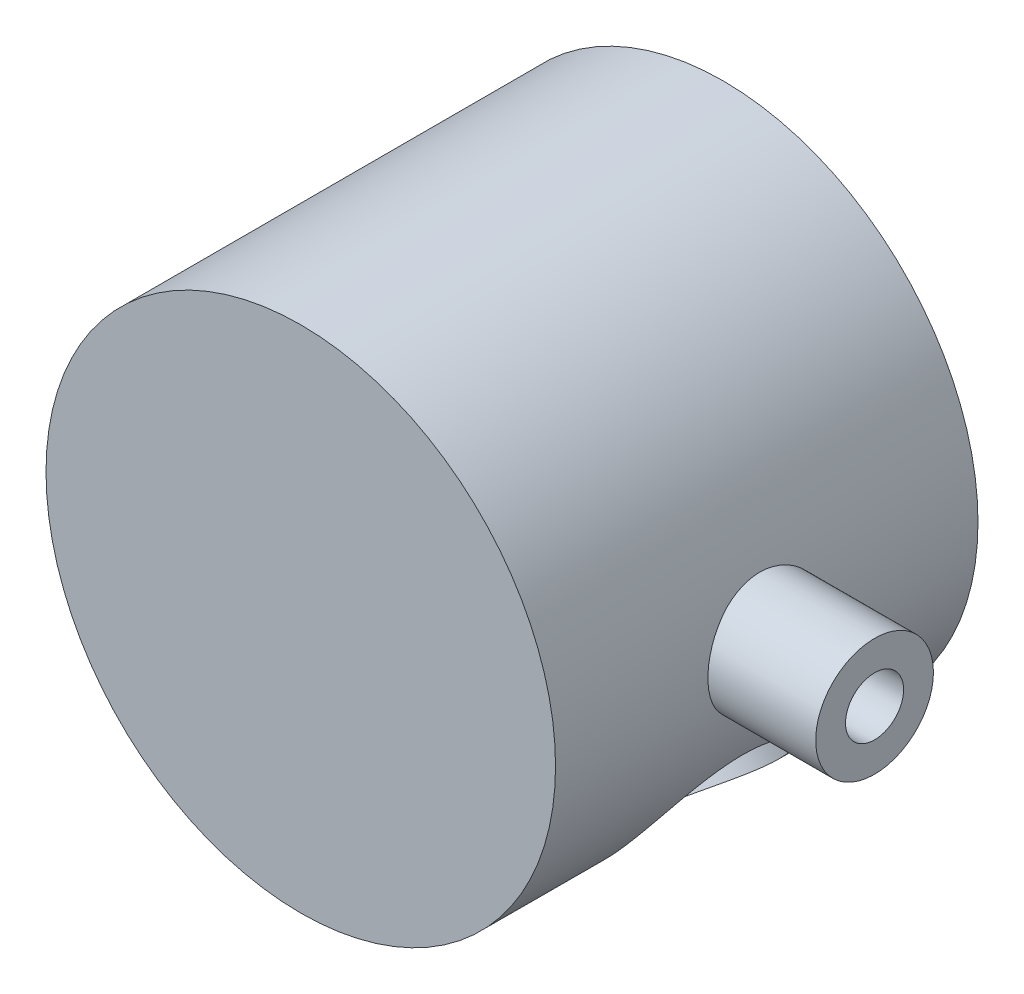
SolidWorks part; units mm, degrees
ref_plane "Ebene vorne" through (0, 0, 0) normal (0, 0, 1) x (1, 0, 0)
ref_plane "Ebene oben" through (0, 0, 0) normal (0, 1, 0) x (1, 0, 0)
ref_plane "Ebene rechts" through (0, 0, 0) normal (1, 0, 0) x (0, 0, -1)
sketch "Sketch1" plane through (0, 0, 0) normal (0, 0, 1) x (1, 0, 0)
  circle A1 centre (0, 0) radius 24.123
  dimension "D3" = 48.246
extrude "Boss-Extrude1" add sketch "Sketch1" along normal blind 35 and the other way blind 5
sketch "Sketch2" plane through (0, 0, 0) normal (1, 0, 0) x (0, 0, -1)
  line L0 (0, 24.123) -> (0, -24.123) construction
  circle A0 centre (-15, 0) radius 3.25
  dimension "D1" = 15
  dimension "D2" = 6.5
extrude "Cut-Extrude2" cut sketch "Sketch2" along normal blind 19.25
sketch "Sketch7" plane through (0, 0, -5) normal (0, 0, -1) x (-1, 0, 0)
  circle A0 centre (0, 0) radius 17.25
  dimension "D1" = 34.5
extrude "Cut-Extrude10" cut sketch "Sketch7" against normal blind 30
sketch "Sketch8" plane through (0, 0, 0) normal (1, 0, 0) x (0, 0, -1)
  circle A0 centre (-15, 0) radius 2.75
  dimension "D1" = 5.5
extrude "Cut-Extrude11" cut sketch "Sketch8" along normal blind 24.873 from offset 19.25
sketch "Sketch9" plane through (0, 0, 0) normal (1, 0, 0) x (0, 0, -1)
  circle A0 centre (-15, 0) radius 5.575
extrude "Boss-Extrude2" add sketch "Sketch9" along normal blind 11.203 from offset 23.125 separate body
extrude "Cut-Extrude12" cut sketch "Sketch8" along normal blind 50
sketch "Sketch14" plane through (0, 0, 0) normal (0, 1, 0) x (1, 0, 0)
  line L0 (0, 5) -> (0, -35) construction
  line L1 (17.25, 5) -> (-17.25, 5) construction
  line L2 (-24.123, -35) -> (24.123, -35) construction
ref_plane "Plane1" through (0, 0, 0) normal (-0.7071, 0.7071, 0) x (0.7071, 0.7071, 0)
sketch "Sketch4" plane through (0, 0, 0) normal (-0.7071, 0.7071, 0) x (0.7071, 0.7071, 0)
  line L2 (24.123, 5) -> (-24.123, 5) construction
  circle A0 centre (0, -15) radius 2.75
  dimension "D2" = 20
extrude "Cut-Extrude3" cut sketch "Sketch4" against normal blind 200
sketch "Sketch6" plane through (0, 0, 0) normal (-0.7071, 0.7071, 0) x (0.7071, 0.7071, 0)
  line L2 (24.123, 5) -> (-24.123, 5) construction
  circle A0 centre (0, -15) radius 5.25
  dimension "D1" = 20
  dimension "D2" = 10.5
extrude "Cut-Extrude9" cut sketch "Sketch6" along normal blind 4.533 from offset 24.123 offset against normal yes
sketch "Sketch12" plane through (0, 0, 0) normal (-0.7071, 0.7071, 0) x (0.7071, 0.7071, 0)
  circle A0 centre (0, -15) radius 8.25
  dimension "D1" = 16.5
extrude "Cut-Extrude14" cut sketch "Sketch12" along normal blind 2 from offset 24.125 offset against normal yes
sketch "Sketch13" plane through (0, 0, 0) normal (-0.7071, 0.7071, 0) x (0.7071, 0.7071, 0)
  circle A0 centre (0, -15) radius 3.25
  dimension "D1" = 6.5
extrude "Cut-Extrude15" cut sketch "Sketch13" against normal blind 19.09
pattern_circular "CirPattern3" count 2 over 90 about axis through (0, 0, -5) along (0, 0, -1) of "Cut-Extrude3", "Cut-Extrude9", "Cut-Extrude14", "Cut-Extrude15"
